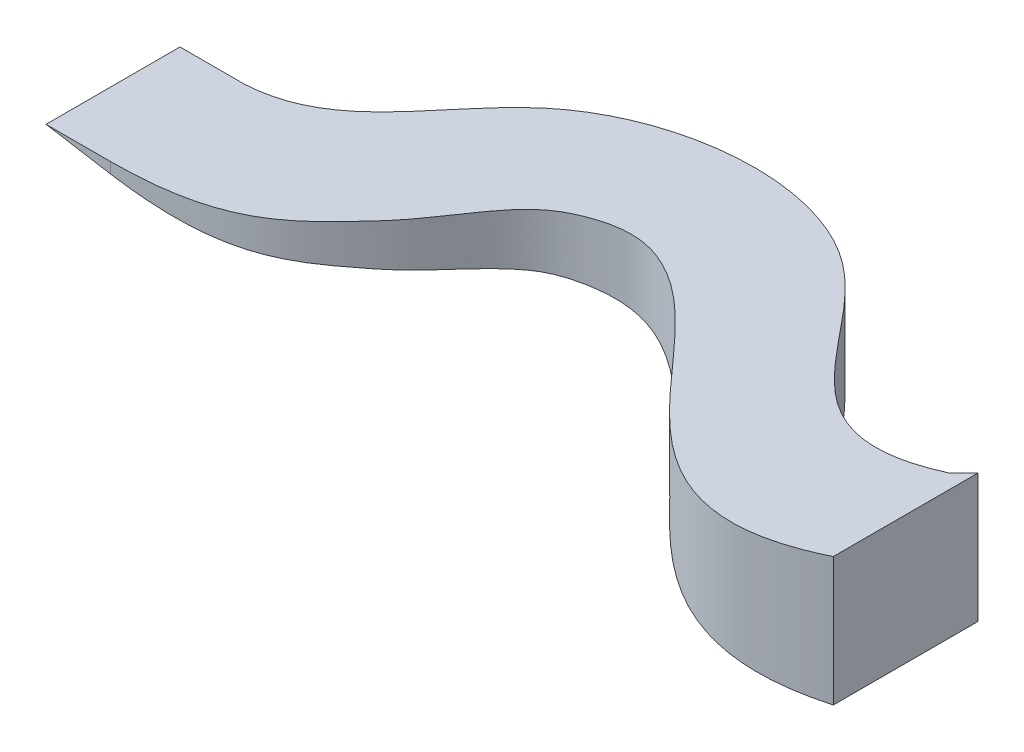
SolidWorks part; units mm, degrees
ref_plane "Front Plane" through (0, 0, 0) normal (0, 0, 1) x (1, 0, 0)
ref_plane "Top Plane" through (0, 0, 0) normal (0, 1, 0) x (1, 0, 0)
ref_plane "Right Plane" through (0, 0, 0) normal (1, 0, 0) x (0, 0, -1)
sketch "Sketch2" plane through (0, 0, 0) normal (0, 1, 0) x (1, 0, 0)
  line L0 (-196.7813, -5) -> (103.2187, -5)
  line L1 (-196.7813, -5) -> (-196.7813, 620) construction
  line L3 (-196.7813, -5) -> (103.2187, -5) construction
  line L5 (2222.8186, 1284.7943) -> (2804.5881, 695.5099)
  line L6 (3386.2389, 760.2462) -> (3386.2389, 85.0661)
  line L10 (3386.2389, 85.0661) -> (3386.2389, 760.2462) construction
  line L11 (988.3751, 402.5548) -> (1372.2317, 851.1327)
  line L12 (2430.1317, 276.9455) -> (1790.5499, 874.4906)
  line L13 (-196.7813, -5) -> (-196.7813, 595)
  line L16 (103.2187, 620) -> (-196.7813, 620)
  line L17 (-196.7813, 620) -> (-196.7813, 595)
  line L18 (920.3448, 1239.1858) -> (495.9912, 789.4197)
  line L19 (2195.0192, 1312.9528) -> (2198.7778, 1309.1456)
  line L20 (3386.2389, 760.2462) -> (3317.0354, 692.0282)
  arc A0 (103.2187, 620) -> (495.9912, 789.4197) centre (103.2187, 1160) ccw
  arc A1 (103.2187, -5) -> (988.3751, 402.5548) centre (103.2187, 1160) ccw
  arc A2 (1790.5499, 874.4906) -> (1372.2317, 851.1327) centre (1592.571, 662.5841) ccw
  arc A4 (2804.5881, 695.5099) -> (3317.0354, 692.0282) centre (3062.5539, 950.1859) ccw
  arc A6 (2431.9635, 275.2341) -> (3386.2389, 85.0661) centre (3062.5539, 950.1859) ccw
  arc A7 (2222.8186, 1284.7943) -> (920.3448, 1239.1858) centre (1592.571, 662.5841) ccw
  dimension "D8" = 2330
  dimension "D9" = 1080
  dimension "D10" = 580
  dimension "D13" = 725
sketch3d "3DSketch1"
  line L0 (3386.2389, 0, -760.2462) -> (3386.2389, 611.9185, -760.2462)
  line L2 (-196.7813, 0, 5) -> (-196.7813, 39.2023, 5)
ref_plane "Plane1" through (0, 0, 0) normal (0, 1, 0) x (1, 0, 0)
sketch "Sketch3" plane through (0, 0, 0) normal (0, 1, 0) x (1, 0, 0)
  line L0 (103.2187, 620) -> (-196.7813, 620)
  line L1 (-196.7813, 620) -> (-196.7813, -5)
  line L2 (-196.7813, -5) -> (103.2187, -5)
  line L3 (3386.2389, 85.0661) -> (3386.2389, 760.2462)
  spline S0 degree 3 poles (103.2187, -5) (588.1952, -3.1639) (771.9646, 163.7992) (1094.0727, 516.9613) (1231.5566, 783.163) (1553.4618, 941.6944) (2236.259, 839.9545) (2563.0648, -321.1586) (3386.2389, 85.0661) knots 0 0 0 0 0.16919 0.199378 0.290494 0.314772 0.430766 1 1 1 1
  spline S1 degree 1 poles (3386.2389, 760.2462) (3317.0354, 692.0282) knots 0 0 1 1
  spline S2 degree 3 poles (3317.0354, 692.0282) (2719.2854, 421.3433) (2458.9586, 1613.401) (791.3452, 1472.7107) (517.504, 642.6496) (103.2187, 620) knots 0 0 0 0 0.371434 0.71736 1 1 1 1
extrude "Boss-Extrude1" add sketch "Sketch3" along normal blind 600
sketch "Sketch5" plane through (0, 0, 0) normal (0, 0, 1) x (1, 0, 0)
  line L0 (3386.2389, 0) -> (-196.7813, 600)
  line L1 (-196.7813, 600) -> (-196.7813, 0)
  line L2 (-196.7813, 0) -> (3386.2389, 0)
extrude "Cut-Extrude5" cut sketch "Sketch5" against normal blind 2000 and the other way blind 2000
